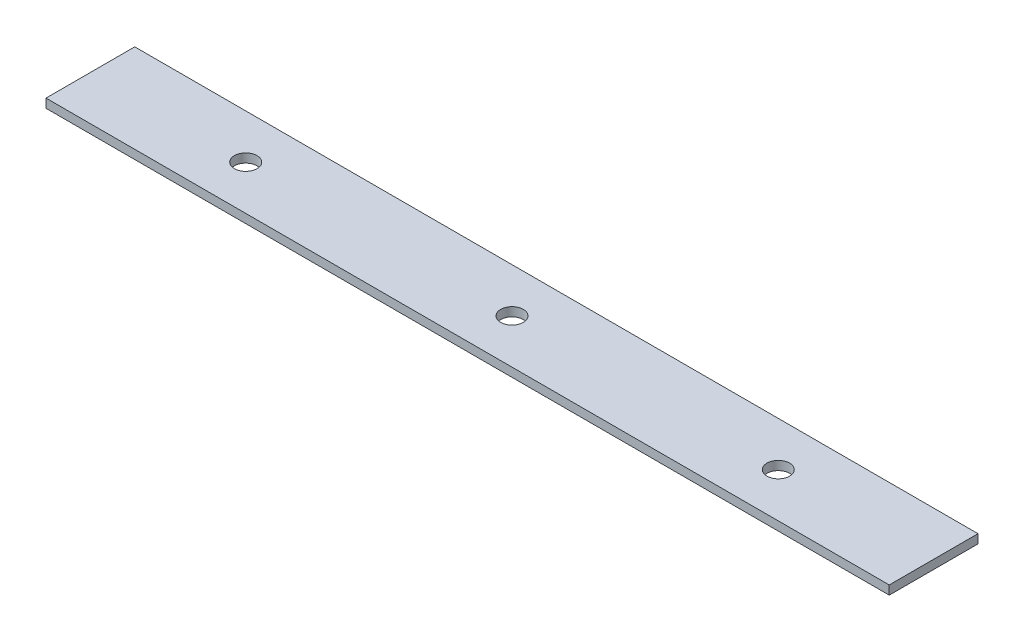
SolidWorks part; units mm, degrees
ref_plane "Front Plane" through (0, 0, 0) normal (0, 0, 1) x (1, 0, 0)
ref_plane "Top Plane" through (0, 0, 0) normal (0, 1, 0) x (1, 0, 0)
ref_plane "Right Plane" through (0, 0, 0) normal (1, 0, 0) x (0, 0, -1)
sketch "Sketch1" plane through (0, 0, 0) normal (0, 1, 0) x (1, 0, 0)
  line L0 (0, 12.7) -> (241.3, 12.7) construction
  line L1 (0, 0) -> (241.3, 0)
  line L2 (0, 0) -> (0, 25.4)
  line L3 (0, 25.4) -> (241.3, 25.4)
  line L4 (241.3, 0) -> (241.3, 25.4)
  circle A0 centre (196.85, 12.7) radius 3.2385
  circle A1 centre (120.65, 12.7) radius 3.2385
  circle A2 centre (44.45, 12.7) radius 3.2385
  dimension "D5" = 6.477
  dimension "D1" = 76.2
  dimension "D2" = 241.3
  dimension "D3" = 25.4
  dimension "D4" = 76.2
extrude "Boss-Extrude1" add sketch "Sketch1" along normal blind 2.54
